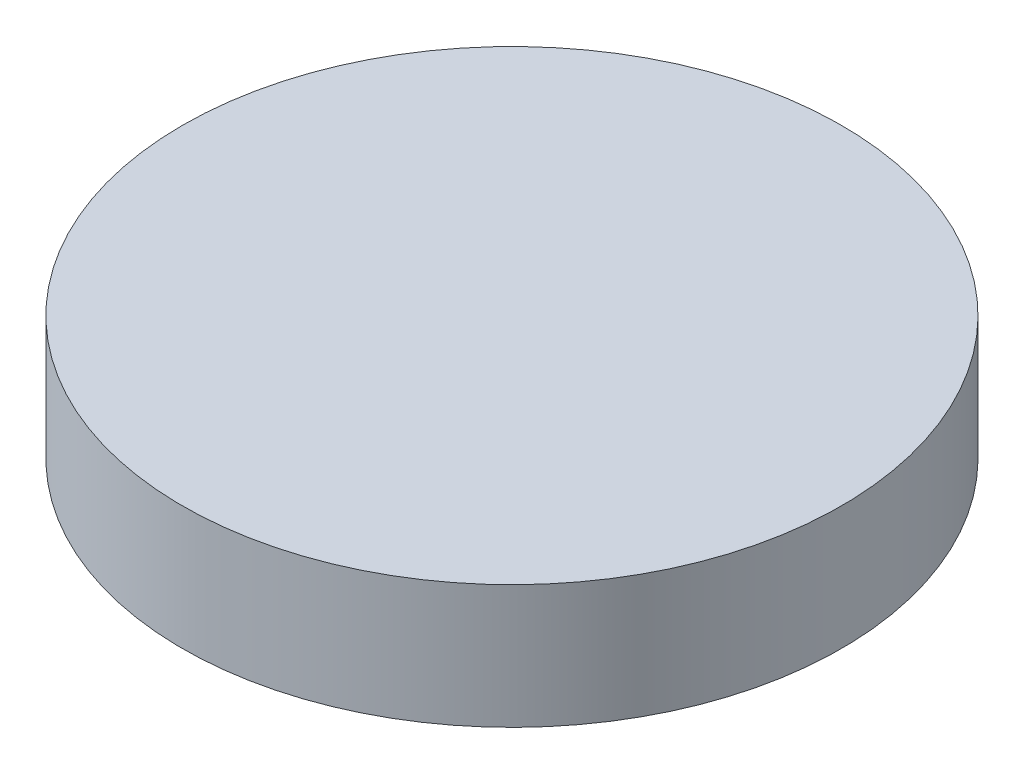
SolidWorks part; units mm, degrees
material "Glass"
ref_plane "Front Plane" through (0, 0, 0) normal (0, 0, 1) x (1, 0, 0)
ref_plane "Top Plane" through (0, 0, 0) normal (0, 1, 0) x (1, 0, 0)
ref_plane "Right Plane" through (0, 0, 0) normal (1, 0, 0) x (0, 0, -1)
sketch "Sketch1" plane through (0, 0, 0) normal (0, 0, 1) x (1, 0, 0)
  line L0 (0, 0) -> (-12.7, 0)
  line L1 (-12.7, 0) -> (-12.7, 4.7625)
  line L2 (-12.7, 4.7625) -> (0, 4.7625)
  line L3 (0, 4.7625) -> (0, 0)
  dimension "D1" = 12.7
  dimension "D3" = 4.7625
revolve "Revolve1" add sketch "Sketch1" angle 360 about L3
